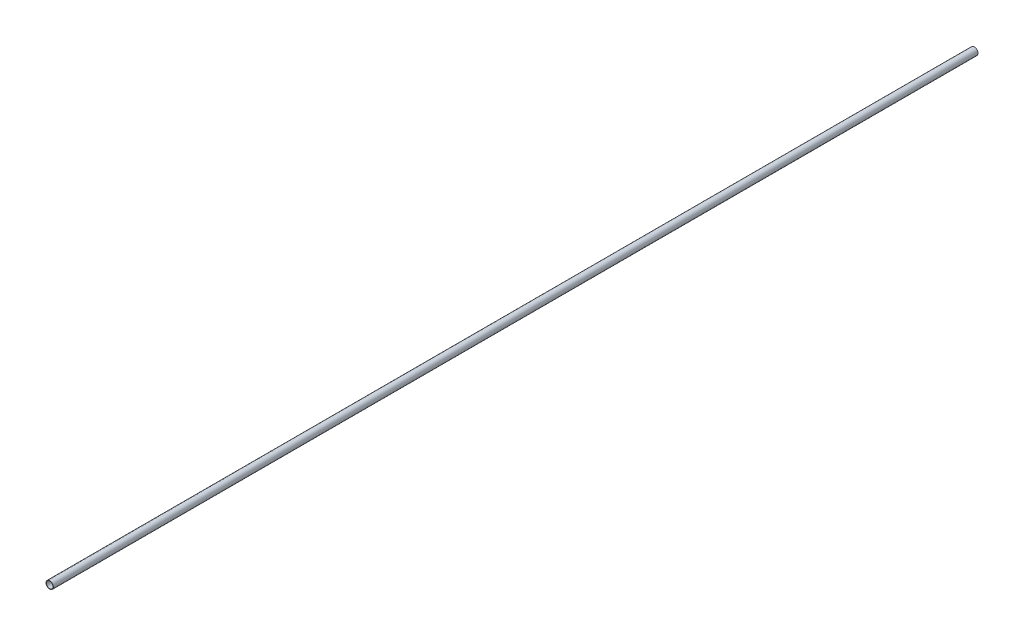
SolidWorks part; units mm, degrees
material "carbon fiber"
ref_plane "Front Plane" through (0, 0, 0) normal (0, 0, 1) x (1, 0, 0)
ref_plane "Top Plane" through (0, 0, 0) normal (0, 1, 0) x (1, 0, 0)
ref_plane "Right Plane" through (0, 0, 0) normal (1, 0, 0) x (0, 0, -1)
sketch "Эскиз1" plane through (0, 0, 0) normal (0, 0, 1) x (1, 0, 0)
  circle A0 centre (0, 0) radius 8
  circle A1 centre (0, 0) radius 7
  dimension "D1" = 16
  dimension "D2" = 1
extrude "Бобышка-Вытянуть1" add sketch "Эскиз1" along normal mid plane 2000
